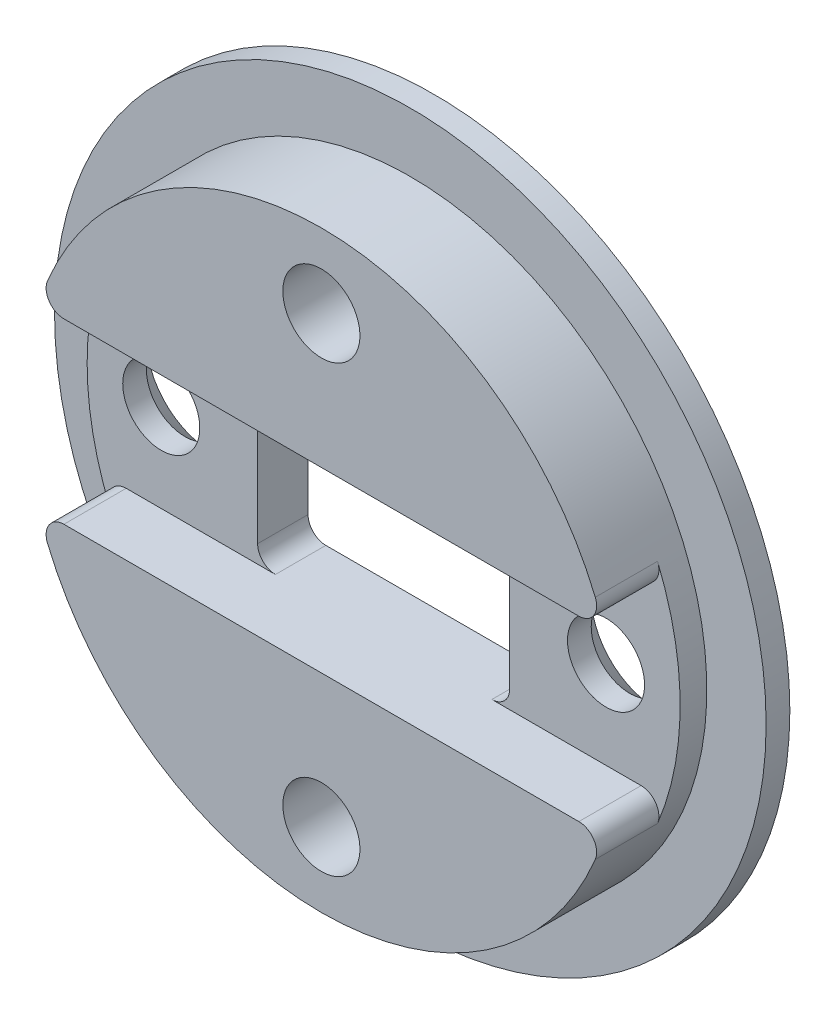
SolidWorks part; units mm, degrees
material "ABS"
ref_plane "Ebene vorne" through (0, 0, 0) normal (0, 0, 1) x (1, 0, 0)
ref_plane "Ebene oben" through (0, 0, 0) normal (0, 1, 0) x (1, 0, 0)
ref_plane "Ebene rechts" through (0, 0, 0) normal (1, 0, 0) x (0, 0, -1)
sketch "Skizze2" plane through (0, 0, 0) normal (0, 1, 0) x (1, 0, 0)
  line L0 (0, 0) -> (10, 0)
  line L2 (10, 0) -> (10, 3)
  line L3 (10, 3) -> (12, 3)
  line L4 (12, 3) -> (12, 3.8)
  line L5 (12, 3.8) -> (0, 3.8)
  line L6 (0, 3.8) -> (0, 0)
  dimension "D1" = 3
  dimension "D2" = 2
  dimension "D3" = 0.8
  dimension "D4" = 10
revolve "Rotation1" add sketch "Skizze2" angle 360 about L6
sketch "Skizze14" plane through (0, 0, 0) normal (0, 0, 1) x (1, 0, 0)
  line L1 (-4.25, -3) -> (4.25, -3)
  line L2 (-4.25, -3) -> (-4.25, 3)
  line L3 (-4.25, 3) -> (4.25, 3)
  line L4 (4.25, -3) -> (4.25, 3)
  line L5 (-4.25, -3) -> (4.25, 3) construction
  line L6 (-4.25, 3) -> (4.25, -3) construction
  point P0 (0, 0)
  dimension "D1" = 6
  dimension "D2" = 8.5
extrude "Schnitt-Linear austragen4" cut sketch "Skizze14" against normal through all
sketch "Skizze15" plane through (0, 0, 0) normal (0, 0, 1) x (1, 0, 0)
  line L0 (4.25, 3) -> (-4.25, 3) construction
  line L1 (12, -3) -> (-12, -3)
  line L2 (12, -3) -> (12, 3)
  line L3 (12, 3) -> (-12, 3)
  line L4 (-12, -3) -> (-12, 3)
  line L5 (12, -3) -> (-12, 3) construction
  line L6 (12, 3) -> (-12, -3) construction
  circle A0 centre (0, 0) radius 12 construction
  point P0 (0, 0)
extrude "Schnitt-Linear austragen5" cut sketch "Skizze15" against normal offset from surface (2.1 mm away) 0.9 up to face at (-12, 0, -3)
fillet "Verrundung1" radius 0.6 4 edges at (-4.25, -3, -2.95) (4.25, 3, -2.95) (4.25, -3, -2.95) (-4.25, 3, -2.95)
fillet "Verrundung2" radius 0.6 4 edges at (-9.5394, 3, -1.05) (9.5394, 3, -1.05) (9.5394, -3, -1.05) (-9.5394, -3, -1.05)
hole_wizard "Formsenkung für M2 Linsensenkschraube mit Schlitz1" positions "Skizze16" profile "Skizze18" countersink size "M2" standard "DIN" end condition through all
sketch "Skizze16" plane through (0, 0, -3.8) normal (0, 0, 1) x (1, 0, 0)
  point P0 (-7.5, 0)
  point P2 (7.5, 0)
  dimension "D1" = 7.5
  dimension "D2" = 7.5
sketch "Skizze18" plane through (-7.5, 0, -3.8) normal (1, 0, 0) x (0, 1, 0)
  line L0 (0, 0) -> (0, 3.8)
  line L1 (0, 3.8) -> (1.3, 3.8)
  line L2 (1.3, 3.8) -> (1.3, 0.9)
  line L3 (1.3, 0.9) -> (2.2, 0)
  line L5 (2.2, 0) -> (0, 0)
  line L6 (-1.3, 0.9) -> (-2.2, 0) construction
  line L11 (0, -6.35) -> (0, 107.95) construction
  dimension "Bohrerdurchmesser" = 2.6
  dimension "Bohrungstiefe" = 3.8
  dimension "Senkdurchmesser (Oben)" = 4.4
  dimension "Senkwinkel (Oben)" = 90
sketch "Skizze23" plane through (0, 0, -3.8) normal (0, 0, -1) x (-1, 0, 0)
  point P0 (0, 7.5)
  point P2 (0, -7.5)
  dimension "D1" = 7.5
  dimension "D2" = 7.5
hole_wizard "Formsenkung für M2 Linsensenkschraube mit Schlitz2" positions "Skizze23" profile "Skizze25" countersink size "M2" standard "DIN" end condition through all
sketch "Skizze25" plane through (0, 7.5, -3.8) normal (1, 0, 0) x (0, 1, 0)
  line L0 (0, 0) -> (0, 3.8)
  line L1 (0, 3.8) -> (1.3, 3.8)
  line L2 (1.3, 3.8) -> (1.3, 0.9)
  line L3 (1.3, 0.9) -> (2.2, 0)
  line L5 (2.2, 0) -> (0, 0)
  line L6 (-1.3, 0.9) -> (-2.2, 0) construction
  line L11 (0, -6.35) -> (0, 107.95) construction
  dimension "Bohrerdurchmesser" = 2.6
  dimension "Bohrungstiefe" = 3.8
  dimension "Senkdurchmesser (Oben)" = 4.4
  dimension "Senkwinkel (Oben)" = 90
